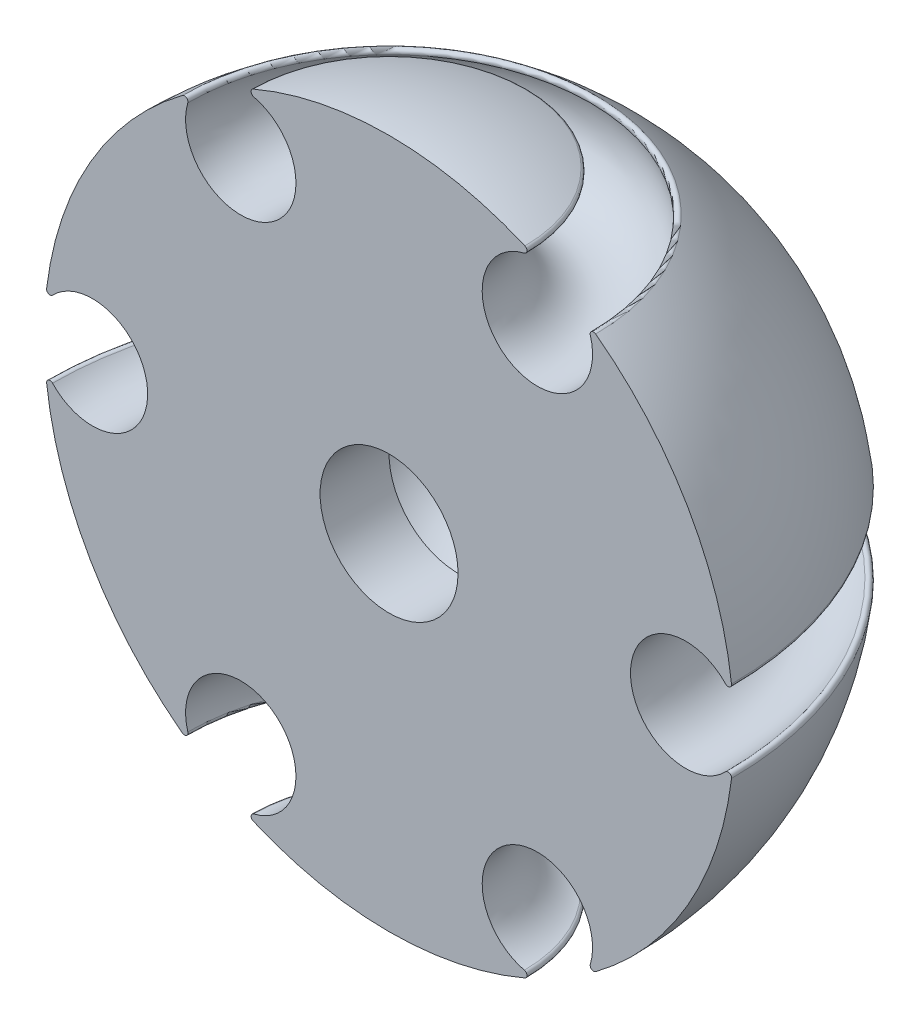
SolidWorks part; units mm, degrees
ref_plane "Front Plane" through (0, 0, 0) normal (0, 0, 1) x (1, 0, 0)
ref_plane "Top Plane" through (0, 0, 0) normal (0, 1, 0) x (1, 0, 0)
ref_plane "Right Plane" through (0, 0, 0) normal (1, 0, 0) x (0, 0, -1)
sketch "Sketch1" plane through (0, 0, 0) normal (0, 0, 1) x (1, 0, 0)
  line L1 (0, 47.6582) -> (0, 137.5861) construction
  line L2 (0, 100) -> (0, 0)
  line L3 (1043, 50) -> (35, 50) construction
  line L8 (0, 50) -> (-1000, 50) construction
  line L10 (25, 50) -> (22, 50) construction
  line L11 (0, 50) -> (21.5, 87.2391) construction
  line L12 (21.5, 12.7609) -> (0, 50) construction
  arc A2 (0, 100) -> (19.6922, 95.9589) centre (0, 50) cw
  arc A3 (48.7893, 55.5212) -> (48.7893, 44.4788) centre (43, 50) ccw
  arc A5 (29.1762, 10.5078) -> (19.6132, 4.9866) centre (21.5, 12.7609) ccw
  arc A6 (19.6132, 95.0134) -> (29.1762, 89.4922) centre (21.5, 87.2391) ccw
  arc A7 (29.9555, 90.0334) -> (49.6476, 55.9255) centre (0, 50) cw
  arc A8 (49.6476, 44.0745) -> (29.9555, 9.9666) centre (0, 50) cw
  arc A9 (19.6922, 4.0411) -> (0, 0) centre (0, 50) cw
  arc A10 (19.6922, 95.9589) -> (19.6132, 95.0134) centre (19.4952, 95.4993) cw
  arc A11 (29.9555, 90.0334) -> (29.1762, 89.4922) centre (29.6559, 89.633) ccw
  arc A12 (29.9555, 9.9666) -> (29.1762, 10.5078) centre (29.6559, 10.367) cw
  arc A13 (19.6922, 4.0411) -> (19.6132, 4.9866) centre (19.4952, 4.5007) ccw
  arc A14 (49.6476, 44.0745) -> (48.7893, 44.4788) centre (49.1512, 44.1337) ccw
  arc A15 (49.6476, 55.9255) -> (48.7893, 55.5212) centre (49.1512, 55.8663) cw
  point P15 (0.0161, 49.9907)
  point P18 (0.7356, 50.4247)
  point P26 (28.5265, 91.0639)
  point P31 (28.5265, 8.9361)
  point P34 (49.8256, 45.8273)
  dimension "D1" = 0.5
  dimension "D2" = 100
  dimension "D3" = 16
  dimension "D6" = 2
  dimension "D7" = 2
  dimension "D12" = 60
  dimension "D10" = 60
  dimension "D8" = 0.5
  dimension "D9" = 0.5
  dimension "D4" = 50
  dimension "D5" = 43
  dimension "D11" = 43
  dimension "D13" = 43
revolve "Revolve2" add sketch "Sketch1" angle 180 about L1
sketch "Sketch2" plane through (0, 0, 0) normal (0, 0, 1) x (1, 0, 0)
  line L0 (0, 101.9351) -> (0, 91.5481) construction
  line L1 (-62.0558, 50) -> (45.6762, 50) construction
  circle A0 centre (0, 50) radius 10
  dimension "D1" = 20
  dimension "D2" = 50
  dimension "D3" = 50
extrude "Cut-Extrude1" cut sketch "Sketch2" against normal blind 10
ref_plane "Plane1" through (0, 50, 0) normal (0, 1, 0) x (1, 0, 0)
sketch "Sketch5" plane through (0, 50, 0) normal (0, 1, 0) x (1, 0, 0)
  line L0 (0, 25) -> (0, 10)
  line L1 (0, 10) -> (15, 10)
  line L2 (0, 0) -> (0, 35.4652) construction
  arc A0 (0, 25) -> (15, 10) centre (0, 10) cw
  dimension "D3" = 15
  dimension "D1" = 10
  dimension "D2" = 15
revolve "Cut-Revolve2" cut sketch "Sketch5" angle 360 about L2
